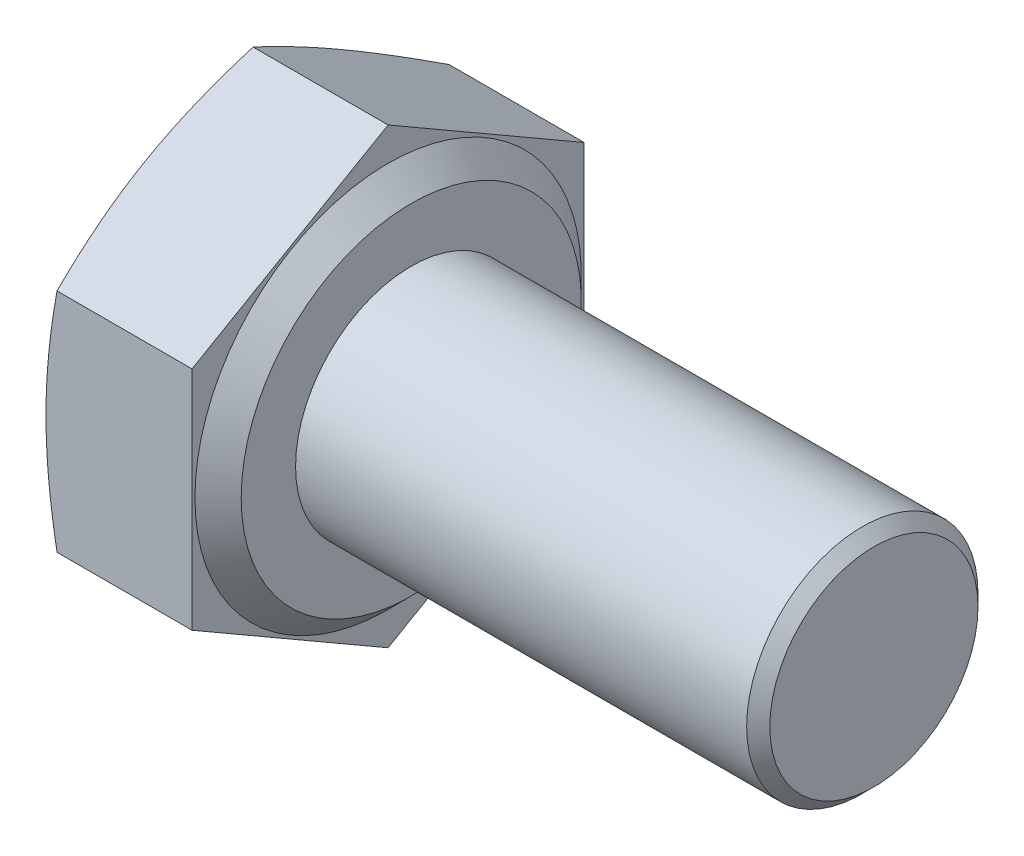
SolidWorks part; units mm, degrees
ref_plane "Front" through (0, 0, 0) normal (0, 0, 1) x (1, 0, 0)
ref_plane "Top" through (0, 0, 0) normal (0, 1, 0) x (1, 0, 0)
ref_plane "Right" through (0, 0, 0) normal (1, 0, 0) x (0, 0, -1)
sketch "Sketch2" plane through (0, 0, 0) normal (1, 0, 0) x (0, 0, -1)
  line L1 (3.39, -1.9572) -> (3.39, 1.9572)
  line L2 (3.39, 1.9572) -> (0, 3.9144)
  line L3 (0, 3.9144) -> (-3.39, 1.9572)
  line L4 (-3.39, 1.9572) -> (-3.39, -1.9572)
  line L5 (-3.39, -1.9572) -> (0, -3.9144)
  line L6 (0, -3.9144) -> (3.39, -1.9572)
  circle A0 centre (0, 0) radius 3.39 construction
  dimension "s" = 6.78
extrude "BaseHead" add sketch "Sketch2" along normal blind 2.925
sketch "Sketch3" plane through (0, 0, 0) normal (0, 0, 1) x (1, 0, 0)
  line L0 (2.925, 3.9144) -> (2.925, 2.94)
  line L2 (2.925, 2.94) -> (2.525, 3.34)
  line L3 (2.525, 3.34) -> (2.525, 3.9144)
  line L5 (2.525, 3.9144) -> (2.925, 3.9144)
  line L6 (-0.9571, 0) -> (7.6478, 0) construction
  line L7 (2.925, 3.9144) -> (0, 3.9144) construction
  dimension "D1" = 45
  dimension "c" = 0.4
  dimension "Dw" = 5.88
revolve "BearingFace" cut sketch "Sketch3" angle 360 about L6
sketch "Sketch4" plane through (0, 0, 0) normal (0, 0, 1) x (1, 0, 0)
  line L0 (-0.4935, 0) -> (3.5626, 0) construction
  line L2 (0, 3.9144) -> (0.1909, 3.9144)
  line L4 (0.1909, 3.9144) -> (0, 3.39)
  line L6 (0, 3.39) -> (0, 3.9144)
  line L7 (2.525, 3.9144) -> (0, 3.9144) construction
  dimension "D1" = 20
  dimension "D2" = 6.78
revolve "HeadChamfer" cut sketch "Sketch4" angle 360 about L0
sketch "Sketch5" plane through (2.925, 0, 0) normal (1, 0, 0) x (0, 0, -1)
  circle A0 centre (0, 0) radius 2
  dimension "d" = 4
extrude "BaseBody" add sketch "Sketch5" along normal blind 8
cosmetic thread "ThreadCosmetic1" parameters "D2"=3.242
chamfer "Chamfer1" distance 0.2 angle 45 1 edges at (10.925, 0, -2)
fillet "HeadFillet" [suppressed] radius 0.2
sketch "Sketch6" plane through (0, 0, 0) normal (0, 0, 1) x (1, 0, 0)
  line L0 (2.925, 2.379) -> (3.304, 2.379)
  line L1 (3.304, 2.379) -> (3.304, 2)
  line L2 (3.304, 2) -> (3.1145, 1.6718)
  line L3 (3.1145, 1.6718) -> (2.925, 2)
  line L4 (2.925, 2) -> (2.925, 2.379)
  line L5 (10.725, 2) -> (2.925, 2) construction
  line L6 (2.925, -2.94) -> (2.925, 2.94) construction
  dimension "D1" = 0.379
revolve "Cut-Revolve10" [suppressed] cut sketch "Sketch6" angle 360 about axis through (-0.9571, 0, 0) along (1, 0, 0)
pattern_linear "LPattern10" [suppressed] count 18
equation "\"D2@Sketch4\" = \"s@Sketch2\""
equation "\"D1@Chamfer1\" = 0.05 * \"d@Sketch5\""
equation "\"D1@Sketch6\" =  ( \"d@Sketch5\" - \"D2@ThreadCosmetic1\" )  / 2"
equation "\"pitch@LPattern10\" = \"D1@Sketch6\" * 1.2"
equation "\"D1@LPattern10\" = \"l@BaseBody\" / \"pitch@LPattern10\""
